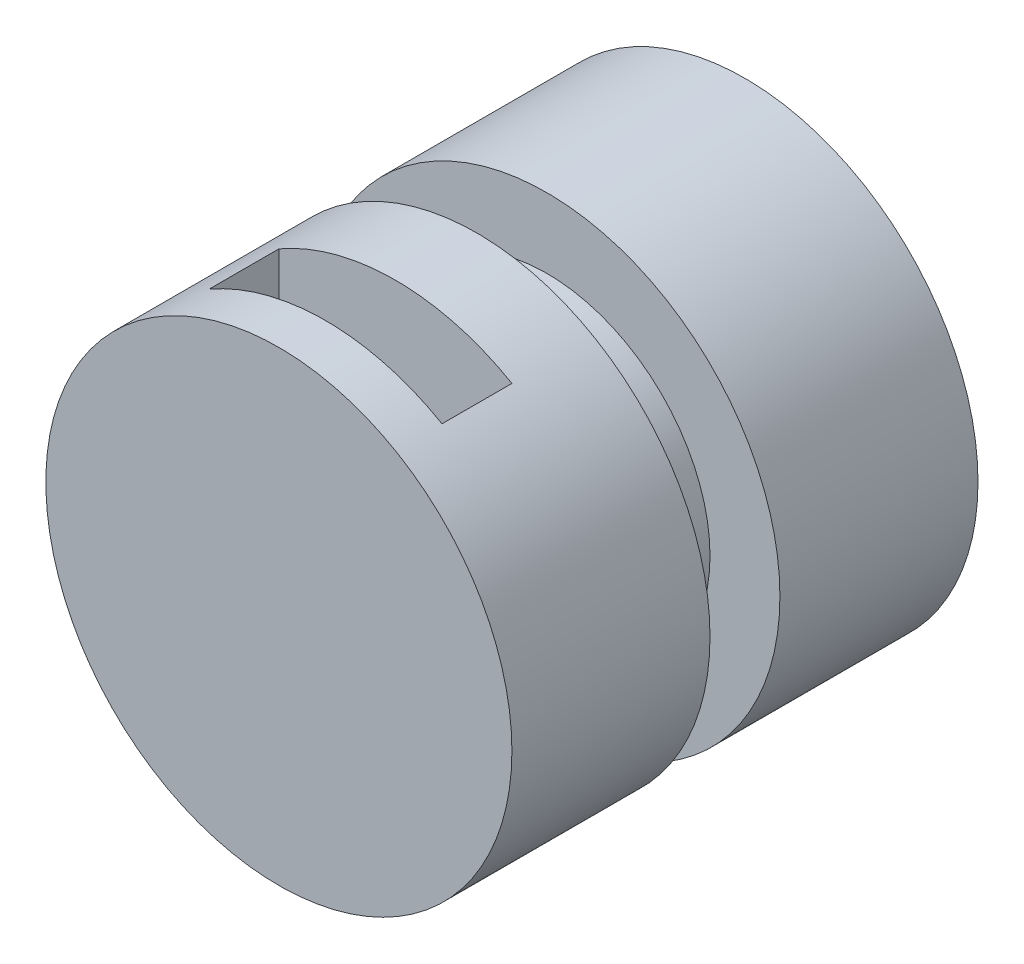
SolidWorks part; units mm, degrees
ref_plane "Front Plane" through (0, 0, 0) normal (0, 0, 1) x (1, 0, 0)
ref_plane "Top Plane" through (0, 0, 0) normal (0, 1, 0) x (1, 0, 0)
ref_plane "Right Plane" through (0, 0, 0) normal (1, 0, 0) x (0, 0, -1)
sketch "Sketch1" plane through (0, 0, 0) normal (0, 1, 0) x (1, 0, 0)
  line L1 (0, -2000) -> (-1000, -2000)
  line L2 (0, -2000) -> (0, 0)
  line L3 (0, 0) -> (-1000, 0)
  line L4 (-1000, -2000) -> (-1000, 0)
  line L5 (0, -2000) -> (-1000, 0) construction
  line L6 (0, 0) -> (-1000, -2000) construction
  point P5 (-500, -1000)
  point P6 (-1000, -871.294)
  point P8 (0, 0)
  point P9 (-1000, -95.1546)
  point P10 (-1000, 0)
  point P11 (-1000, 21.1085)
  point P12 (0, 0)
  point P13 (0, 0)
  dimension "D1" = 1000
  dimension "D2" = 2000
revolve "Revolve1" add sketch "Sketch1" angle 360 about L2
sketch "Sketch4" plane through (0, 0, 0) normal (0, 1, 0) x (1, 0, 0)
  line L0 (-1000, -2000) -> (1000, -2000) construction
  line L1 (500, -1800) -> (-500, -1800)
  line L2 (500, -1800) -> (500, -1500)
  line L3 (500, -1500) -> (-500, -1500)
  line L4 (-500, -1800) -> (-500, -1500)
  line L5 (500, -1800) -> (-500, -1500) construction
  line L6 (500, -1500) -> (-500, -1800) construction
  line L13 (0, -2000) -> (0, 0) construction
  point P4 (0, -1650)
  dimension "D1" = 300
  dimension "D2" = 1000
  dimension "D3" = 200
extrude "Cut-Extrude1" cut sketch "Sketch4" against normal through all both and the other way through all
sketch "Sketch5" plane through (0, 0, 0) normal (0, 1, 0) x (1, 0, 0)
  line L0 (-1000, -2000) -> (-1000, 0) construction
  line L1 (-1000, -850) -> (-700, -850)
  line L2 (-1000, -850) -> (-1000, -1150)
  line L3 (-1000, -1150) -> (-700, -1150)
  line L4 (-700, -850) -> (-700, -1150)
  line L5 (-1000, -850) -> (-700, -1150) construction
  line L6 (-1000, -1150) -> (-700, -850) construction
  line L7 (0, -2000) -> (-1000, -2000) construction
  point P4 (-850, -1000)
  dimension "D1" = 300
  dimension "D2" = 300
  dimension "D3" = 1000
revolve "Cut-Revolve1" cut sketch "Sketch5" angle 360 about L2
